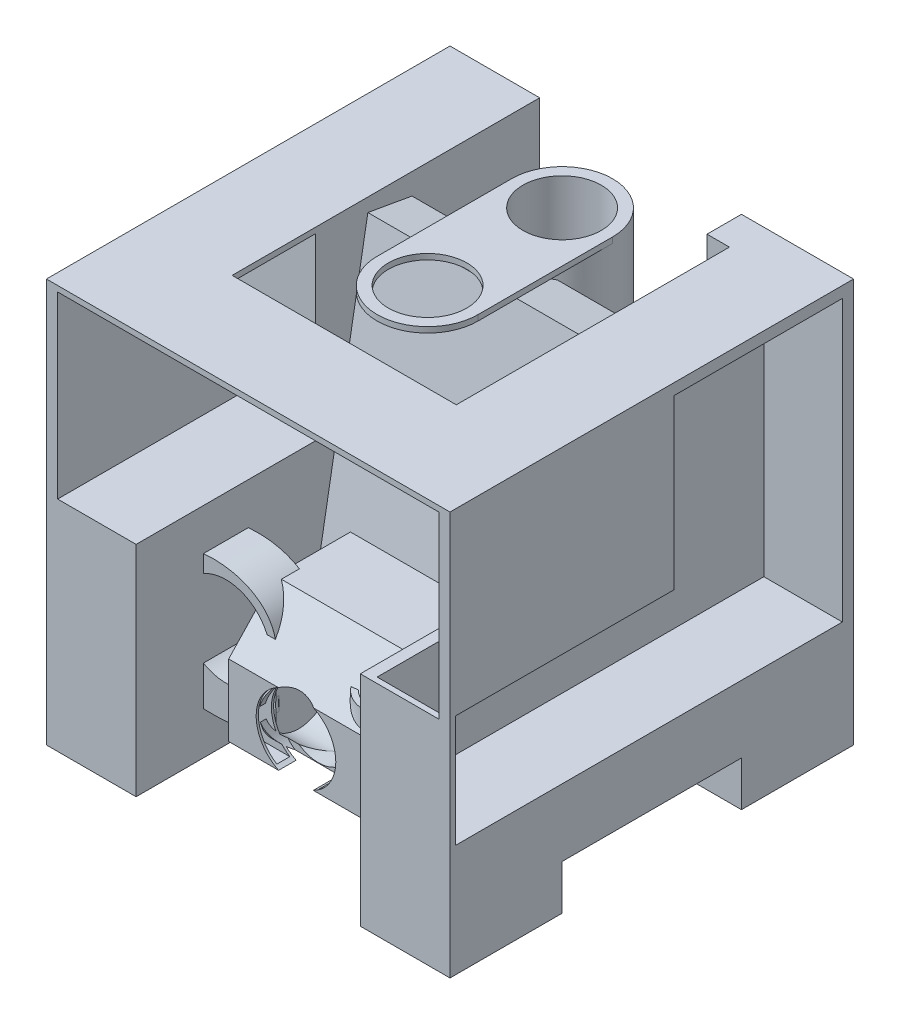
SolidWorks part; units mm, degrees
ref_plane "Front Plane" through (0, 0, 0) normal (0, 0, 1) x (1, 0, 0)
ref_plane "Top Plane" through (0, 0, 0) normal (0, 1, 0) x (1, 0, 0)
ref_plane "Right Plane" through (0, 0, 0) normal (1, 0, 0) x (0, 0, -1)
sketch "Sketch1" plane through (0, 0, 0) normal (0, 1, 0) x (1, 0, 0)
  line L1 (228.6, -228.6) -> (-228.6, -228.6) construction
  line L2 (228.6, -228.6) -> (228.6, 228.6) construction
  line L3 (228.6, 228.6) -> (-228.6, 228.6) construction
  line L4 (-228.6, -228.6) -> (-228.6, 228.6) construction
  line L5 (228.6, -228.6) -> (-228.6, 228.6) construction
  line L6 (228.6, 228.6) -> (-228.6, -228.6) construction
  line L7 (-228.6, 228.6) -> (-127, 228.6)
  line L8 (-228.6, 228.6) -> (-228.6, -228.6)
  line L9 (-228.6, -228.6) -> (-127, -228.6)
  line L10 (-127, 228.6) -> (-127, -228.6)
  line L11 (228.6, -228.6) -> (127, -228.6)
  line L12 (228.6, -228.6) -> (228.6, 228.6)
  line L13 (228.6, 228.6) -> (127, 228.6)
  line L14 (127, -228.6) -> (127, 228.6)
  point P0 (0, 0)
  dimension "D1" = 101.6
  dimension "D2" = 457.2
extrude "Boss-Extrude1" add sketch "Sketch1" along normal blind 457.2
sketch "Sketch2" plane through (0, 0, 0) normal (0, 1, 0) x (1, 0, 0)
  line L0 (-127, 228.6) -> (-102.2411, 152.4)
  line L1 (88.0591, 183.5971) -> (142.4826, 351.0954) construction
  line L2 (142.4826, 351.0954) -> (0, 454.6151) construction
  line L3 (0, 454.6151) -> (-142.4826, 351.0954) construction
  line L4 (-142.4826, 351.0954) -> (-88.0591, 183.5971) construction
  line L5 (-88.0591, 183.5971) -> (88.0591, 183.5971) construction
  line L6 (-102.2411, 152.4) -> (102.2411, 152.4)
  line L7 (102.2411, 152.4) -> (127, 228.6)
  line L8 (0, 183.5971) -> (0, 152.4) construction
  line L9 (-127, 228.6) -> (-228.6, 228.6) construction
  line L10 (-127, 228.6) -> (-127, 101.6)
  line L11 (-127, -228.6) -> (-127, 228.6) construction
  line L12 (-127, 101.6) -> (127, 101.6)
  line L13 (127, 228.6) -> (127, -228.6) construction
  line L14 (127, 101.6) -> (127, 228.6)
  circle A0 centre (0, 304.8) radius 121.2029 construction
  dimension "D1" = 271.018
  dimension "D2" = 304.8
  dimension "D3" = 76.2
  dimension "D4" = 50.8
extrude "Boss-Extrude2" add sketch "Sketch2" along normal blind 127 separate body
sketch "Sketch3" plane through (0, 0, 0) normal (1, 0, 0) x (0, 0, -1)
  line L0 (8.9672, 7.8704) -> (83.9485, 433.1104)
  line L1 (83.9485, 433.1104) -> (33.9203, 441.9317)
  line L2 (33.9203, 441.9317) -> (-41.061, 16.6917)
  line L3 (-41.061, 16.6917) -> (8.9672, 7.8704)
  line L4 (-228.6, 0) -> (228.6, 0) construction
  dimension "D1" = 50.8
  dimension "D2" = 431.8
  dimension "D3" = 80
extrude "Boss-Extrude3" add sketch "Sketch3" along normal mid plane 254 separate body
sketch "Sketch5" plane through (0, 457.2, 0) normal (0, 1, 0) x (1, 0, 0)
  line L0 (0, 127) -> (0, 0) construction
  line L1 (0, 127) -> (0, -25.4) construction
  line L2 (57.15, 127) -> (57.15, -25.4)
  line L3 (-57.15, 127) -> (-57.15, -25.4)
  circle A0 centre (0, 127) radius 44.45
  circle A1 centre (0, -25.4) radius 44.45
  arc A2 (57.15, 127) -> (-57.15, 127) centre (0, 127) ccw
  arc A3 (-57.15, -25.4) -> (57.15, -25.4) centre (0, -25.4) ccw
  point P6 (0, 50.8)
  dimension "D1" = 88.9
  dimension "D4" = 12.7
  dimension "D2" = 25.4
  dimension "D3" = 127
extrude "Boss-Extrude4" add sketch "Sketch5" along normal blind 6.35 separate body
sketch "Sketch6" plane through (0, 457.2, 0) normal (0, -1, 0) x (1, 0, 0)
  circle A0 centre (0, -127) radius 44.45
  circle A1 centre (0, -127) radius 57.15
  circle A2 centre (0, -127) radius 44.45 construction
  arc A3 (-57.15, -127) -> (57.15, -127) centre (0, -127) ccw construction
extrude "Boss-Extrude5" add sketch "Sketch6" along normal blind 304.8
ref_plane "Plane1" through (0, 0, 127) normal (0, 0, 1) x (1, 0, 0)
sketch "Sketch7" plane through (0, 0, 127) normal (0, 0, 1) x (1, 0, 0)
  line L0 (0, 95.25) -> (0, 0) construction
  line L1 (-44.45, 139.7) -> (18.2539, 139.7) construction
  line L2 (-44.45, 139.7) -> (-44.45, 50.8) construction
  line L3 (-44.45, 50.8) -> (18.2539, 50.8) construction
  line L4 (32.6824, 154.8713) -> (121.4706, 159.3297) construction
  line L5 (-44.45, 95.25) -> (18.2539, 95.25)
  circle A0 centre (0, 95.25) radius 44.45 construction
  arc A1 (18.2539, 139.7) -> (32.6824, 154.8713) centre (18.2539, 154.1467) ccw construction
  arc A2 (18.2539, 50.8) -> (121.4706, 159.3297) centre (18.2539, 154.1467) ccw construction
  arc A3 (18.2539, 95.25) -> (77.0765, 157.1005) centre (18.2539, 154.1467) ccw
  dimension "D1" = 50.8
  dimension "D2" = 88.9
  dimension "D3" = 88.9
sketch "Sketch8" plane through (0, 0, 127) normal (0, 0, 1) x (1, 0, 0)
  line L0 (-44.45, 50.8) -> (18.2539, 50.8) construction
  line L1 (-44.45, 139.7) -> (-44.45, 50.8)
  circle A0 centre (-101.4781, 136.9802) radius 50.8
  spline S0 degree 3 poles (-44.45, 139.7) (-38.1015, 213.4208) (-225.6997, 221.2322) (-177.947, 28.582) (-110.9698, 50.8) (-44.45, 50.8) knots 0 0 0 0 0.43257 0.679076 1 1 1 1
  dimension "D1" = 101.6
extrude "Boss-Extrude6" add sketch "Sketch8" along normal mid plane 50.8 separate body
sketch "Sketch9" plane through (-44.45, 0, 0) normal (1, 0, 0) x (0, 0, -1)
  line L0 (-127, 139.7) -> (-127, 50.8) construction
  circle A0 centre (-127, 95.25) radius 38.1
  circle A1 centre (-127, 95.25) radius 44.45
  dimension "D1" = 88.9
  dimension "D2" = 76.2
sweep "Sweep1" add profiles "Sketch9" path "Sketch7"
sketch "Sketch10" plane through (0, 0, 127) normal (0, 0, 1) x (1, 0, 0)
  circle A0 centre (0, 95.25) radius 38.1
  dimension "D1" = 76.2
extrude "Cut-Extrude4" cut sketch "Sketch10" along normal through all
sketch "Sketch12" plane through (-127, 0, 0) normal (1, 0, 0) x (0, 0, -1)
  line L0 (-228.6, 0) -> (228.6, 0) construction
  line L1 (-304.8, 101.6) -> (-127, 355.6) construction
  line L2 (-228.6, 457.2) -> (-228.6, 0) construction
  line L3 (-127, 355.6) -> (-185.2152, 231.8235) construction
  line L4 (-215.9, 228.6) -> (-106.7993, 152.2295) construction
  line L5 (-228.6, 457.2) -> (228.6, 457.2) construction
  line L6 (-228.6, 457.2) -> (-228.6, 0) construction
  line L7 (-106.7993, 152.2295) -> (110.6714, 0) construction
  line L8 (-228.6, 0) -> (228.6, 0) construction
  line L9 (-304.8, 101.6) -> (-177.8, 50.8) construction
  line L10 (-177.8, 50.8) -> (-96.1948, 144.8064) construction
  line L11 (-185.2152, 231.8235) -> (-96.1948, 144.8064) construction
  circle A0 centre (-304.8, 101.6) radius 101.6
  circle A1 centre (-127, 355.6) radius 101.6
  circle A2 centre (-177.8, 50.8) radius 12.7
  circle A3 centre (-185.2152, 231.8235) radius 12.7
  arc A4 (-112.3083, 255.0678) -> (-205.3116, 122.2061) centre (-96.1948, 144.8064) ccw
  dimension "D1" = 203.2
  dimension "D5" = 25.4
  dimension "D2" = 304.8
  dimension "D3" = 50.8
  dimension "D4" = 50.8
sketch "Sketch13" plane through (228.6, 0, 0) normal (1, 0, 0) x (0, 0, -1)
  line L0 (-228.6, 203.2) -> (25.4, 457.2)
  line L1 (-228.6, 457.2) -> (-228.6, 0) construction
  line L2 (-228.6, 457.2) -> (228.6, 457.2) construction
  line L3 (25.4, 457.2) -> (-228.6, 457.2)
  line L4 (-228.6, 457.2) -> (-228.6, 203.2)
  dimension "D1" = 254
sketch "Sketch14" plane through (-127, 0, 0) normal (1, 0, 0) x (0, 0, -1)
  line L0 (-228.6, 457.2) -> (-228.6, 0) construction
  line L1 (-228.6, 450.85) -> (-25.4, 450.85)
  line L2 (-228.6, 450.85) -> (-228.6, 247.65)
  line L3 (-228.6, 247.65) -> (-25.4, 247.65)
  line L4 (-25.4, 450.85) -> (-25.4, 247.65)
  line L5 (-228.6, 457.2) -> (228.6, 457.2) construction
  dimension "D1" = 6.35
  dimension "D2" = 203.2
  dimension "D3" = 203.2
extrude "Cut-Extrude6" cut sketch "Sketch14" against normal blind 88.9 and the other way blind 342.9
sketch "Sketch15" plane through (-127, 0, 0) normal (1, 0, 0) x (0, 0, -1)
  line L0 (-25.4, 450.85) -> (-228.6, 450.85) construction
  line L1 (-228.6, 457.2) -> (-119.8574, 457.2)
  line L2 (-228.6, 457.2) -> (-228.6, 450.85)
  line L3 (-228.6, 450.85) -> (-119.8574, 450.85)
  line L4 (-119.8574, 457.2) -> (-119.8574, 450.85)
extrude "Boss-Extrude7" add sketch "Sketch15" along normal blind 254
sketch "Sketch16" plane through (228.6, 0, 0) normal (1, 0, 0) x (0, 0, -1)
  line L0 (-222.25, 254) -> (-222.25, 127)
  line L1 (-222.25, 127) -> (215.9, 127)
  line L2 (215.9, 127) -> (215.9, 444.5)
  line L3 (215.9, 444.5) -> (25.4, 444.5)
  line L4 (25.4, 444.5) -> (25.4, 254)
  line L5 (25.4, 254) -> (-222.25, 254)
  line L6 (-228.6, 457.2) -> (228.6, 457.2) construction
  line L7 (228.6, 457.2) -> (228.6, 0) construction
  line L8 (-228.6, 0) -> (228.6, 0) construction
  line L9 (-228.6, 457.2) -> (-228.6, 203.2) construction
  dimension "D1" = 12.7
  dimension "D2" = 12.7
  dimension "D3" = 127
  dimension "D4" = 254
  dimension "D5" = 127
  dimension "D6" = 6.35
extrude "Cut-Extrude7" cut sketch "Sketch16" against normal blind 88.9
sketch "Sketch17" plane through (228.6, 0, 0) normal (1, 0, 0) x (0, 0, -1)
  line L0 (-228.6, 0) -> (228.6, 0) construction
  line L1 (-101.6, 50.8) -> (101.6, 50.8)
  line L2 (-101.6, 50.8) -> (-101.6, 0)
  line L3 (-101.6, 0) -> (101.6, 0)
  line L4 (101.6, 50.8) -> (101.6, 0)
  line L5 (-228.6, 457.2) -> (-228.6, 0) construction
  dimension "D1" = 127
  dimension "D2" = 50.8
extrude "Cut-Extrude9" cut sketch "Sketch17" against normal through all
sketch "Sketch18" plane through (127, 0, 0) normal (-1, 0, 0) x (0, 0, 1)
  line L1 (-228.6, 457.2) -> (-189.5779, 457.2)
  line L2 (-228.6, 457.2) -> (-228.6, 131.3819)
  line L3 (-228.6, 131.3819) -> (-189.5779, 131.3819)
  line L4 (-189.5779, 457.2) -> (-189.5779, 131.3819)
extrude "Boss-Extrude8" add sketch "Sketch18" along normal blind 25.4
sketch "Sketch20" plane through (127, 0, 0) normal (-1, 0, 0) x (0, 0, 1)
  line L0 (39.1255, 163.3216) -> (157.2126, 163.3216) construction
  line L1 (157.2126, 163.3216) -> (157.2126, 55.1098) construction
  line L2 (157.2126, 55.1098) -> (171.9662, 55.1098)
  line L3 (171.9662, 55.1098) -> (171.9662, 186.6327) construction
  line L4 (171.9662, 186.6327) -> (39.1255, 186.6327) construction
  line L5 (39.1255, 186.6327) -> (39.1255, 163.3216)
  line L6 (39.1255, 163.3216) -> (120.2689, 163.3216)
  line L7 (120.2689, 163.3216) -> (157.2126, 124.1608)
  line L8 (157.2126, 124.1608) -> (157.2126, 55.1098)
  line L9 (171.9662, 55.1098) -> (171.9662, 132.5982)
  line L10 (171.9662, 132.5982) -> (120.9911, 186.6327)
  line L11 (120.9911, 186.6327) -> (39.1255, 186.6327)
extrude "Extrude-Thin1" add sketch "Sketch20" along normal blind 203.2 thin
sketch "Sketch21" plane through (0, 0, 174.5062) normal (0, 0, 1) x (1, 0, 0)
  circle A0 centre (0, 93.1929) radius 45.1285
extrude "Cut-Extrude10" cut sketch "Sketch21" against normal blind 25.4
